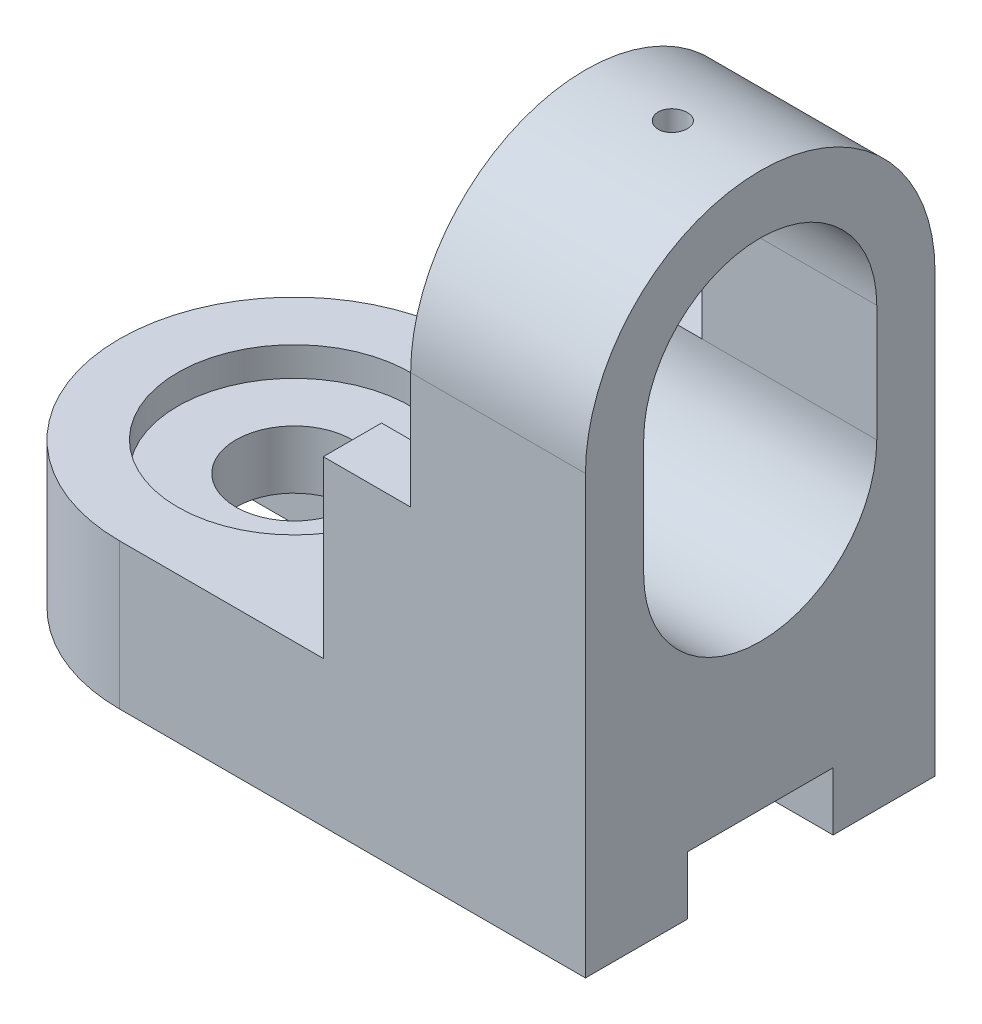
SolidWorks part; units mm, degrees
ref_plane "Front" through (0, 0, 0) normal (0, 0, 1) x (1, 0, 0)
ref_plane "Top" through (0, 0, 0) normal (0, 1, 0) x (1, 0, 0)
ref_plane "Right" through (0, 0, 0) normal (1, 0, 0) x (0, 0, -1)
sketch "Sketch1" plane through (0, 0, 0) normal (0, 1, 0) x (1, 0, 0)
  line L1 (0, -30) -> (80, -30)
  line L3 (0, 30) -> (80, 30)
  line L4 (80, -30) -> (80, 30)
  arc A0 (0, 30) -> (0, -30) centre (0, 0) ccw
  circle A1 centre (0, 0) radius 10
  point P0 (0, 0)
  point P8 (0, 0)
  dimension "D3" = 20
  dimension "D1" = 80
  dimension "D2" = 60
extrude "Boss-Extrude1" add sketch "Sketch1" along normal blind 25
sketch "Sketch2" plane through (80, 0, 0) normal (1, 0, 0) x (0, 0, -1)
  line L0 (-30, 0) -> (30, 0) construction
  line L1 (30, 25) -> (-30, 25)
  line L2 (30, 25) -> (30, 75)
  line L3 (30, 75) -> (-30, 75)
  line L4 (-30, 25) -> (-30, 75)
  line L5 (0, 75) -> (0, 55) construction
  line L6 (20, 75) -> (20, 55)
  line L7 (-20, 75) -> (-20, 55)
  arc A0 (30, 75) -> (-30, 75) centre (0, 75) ccw
  arc A1 (12.9784, 90.2171) -> (-8.969, 92.8761) centre (0, 75) ccw
  arc A2 (20, 75) -> (-20, 75) centre (0, 75) ccw
  arc A3 (-20, 55) -> (20, 55) centre (0, 55) ccw
  point P8 (0, 65)
  line M8 (30, 25) -> (-30, 25)
  dimension "D3" = 20
  dimension "D5" = 20
  dimension "D1" = 60
  dimension "D2" = 75
  dimension "D4" = 20
extrude "Boss-Extrude2" add sketch "Sketch2" against normal blind 45 contours A3 L7 L3 L4 L2 L6 M8 | A2 L3 A0 A1
sketch "Sketch4" plane through (0, 0, 0) normal (0, 0, 1) x (1, 0, 0)
  line L0 (80, 75) -> (80, 0) construction
  line L1 (-30, 0) -> (80, 0)
  line L2 (-30, 0) -> (-30, 10)
  line L3 (-30, 10) -> (80, 10)
  line L4 (80, 0) -> (80, 10)
  dimension "D1" = 10
extrude "Cut-Extrude1" cut sketch "Sketch4" against normal mid plane 25
sketch "Sketch5" plane through (0, 0, 0) normal (0, 0, 1) x (1, 0, 0)
  line L1 (35, 105) -> (50, 105)
  line L2 (35, 105) -> (35, 55)
  line L3 (35, 55) -> (50, 55)
  line L4 (50, 105) -> (50, 55)
  dimension "D1" = 50
  dimension "D2" = 15
extrude "Cut-Extrude2" cut sketch "Sketch5" against normal mid plane 65
sketch "Sketch6" plane through (0, 55, 0) normal (0, 1, 0) x (1, 0, 0)
  line L0 (35, 30) -> (35, -30) construction
  line L1 (35, 15) -> (45, 15)
  line L2 (35, 15) -> (35, -15)
  line L3 (35, -15) -> (45, -15)
  line L4 (45, 15) -> (45, -15)
  point P10 (35, 0)
  dimension "D3" = 30
  dimension "D4" = 10
  dimension "D5" = 0
extrude "Cut-Extrude3" cut sketch "Sketch6" against normal blind 30 and the other way blind 65
sketch "Sketch7" plane through (0, 25, 0) normal (0, 1, 0) x (1, 0, 0)
  circle A0 centre (0, 0) radius 20
  dimension "D1" = 40
extrude "Cut-Extrude4" cut sketch "Sketch7" against normal blind 5
sketch "Sketch9" plane through (0, 55, 0) normal (0, 1, 0) x (1, 0, 0)
  line L0 (80, -30) -> (80, 30) construction
  circle A0 centre (65, 0) radius 2.5
  dimension "D1" = 5
  dimension "D2" = 15
extrude "Cut-Extrude5" cut sketch "Sketch9" along normal blind 55
